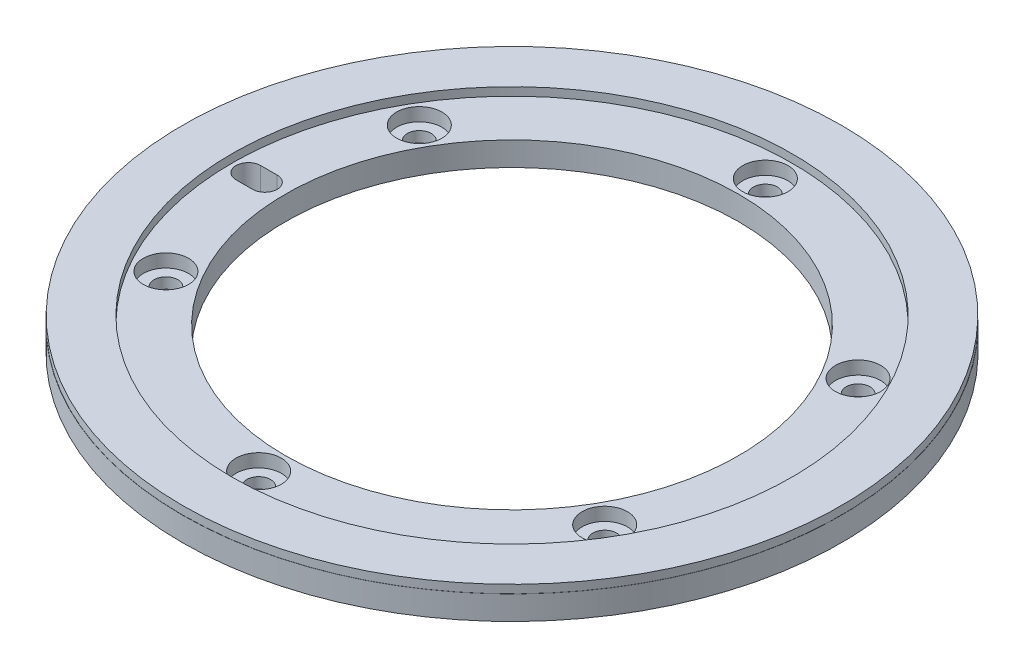
SolidWorks part; units mm, degrees
material "Chrome Stainless Steel"
ref_plane "Front Plane" through (0, 0, 0) normal (0, 0, 1) x (1, 0, 0)
ref_plane "Top Plane" through (0, 0, 0) normal (0, 1, 0) x (1, 0, 0)
ref_plane "Right Plane" through (0, 0, 0) normal (1, 0, 0) x (0, 0, -1)
sketch "Sketch1" plane through (0, 0, 0) normal (0, 0, 1) x (1, 0, 0)
  line L0 (0, -3.2439) -> (0, 13.5479) construction
  line L1 (-27.5, 0) -> (-40, 0)
  line L2 (-27.5, 0) -> (-27.5, 2.9)
  line L3 (-27.5, 2.9) -> (-40, 2.9)
  line L4 (-40, 0) -> (-40, 2.9)
  line L5 (-27.5, 0) -> (0, 0) construction
  dimension "D1" = 55
  dimension "D2" = 80
  dimension "D3" = 2.9
revolve "Revolve1" add sketch "Sketch1" angle 360 about L0
ref_plane "Plane1" through (0, 3.4, 0) normal (0, 1, 0) x (-1, 0, 0)
sketch "Sketch5" plane through (0, 2.9, 0) normal (0, 1, 0) x (1, 0, 0)
  circle A0 centre (0, 0) radius 34
  circle A1 centre (0, 0) radius 39.98
  dimension "D1" = 68
  dimension "D2" = 79.96
hole_wizard "CBORE for M2.5 Hex Socket Head Cap Screw2" positions "Sketch9" profile "Sketch8" counterbore size "M2.5" standard "DIN" end condition through all
sketch "Sketch9" plane through (0, 3.4, 0) normal (0, 1, 0) x (-1, 0, 0)
  line L0 (-46.9378, 0) -> (52.7339, 0) construction
  point P2 (0, -30.75)
  dimension "D1" = 61.5
sketch "Sketch8" plane through (0, 3.4, -30.75) normal (1, 0, 0) x (0, 0, 1)
  line L0 (0, 0) -> (0, 3.4)
  line L1 (0, 3.4) -> (1.45, 3.4)
  line L3 (1.45, 3.4) -> (1.45, 2.1)
  line L4 (1.45, 2.1) -> (2.75, 2.1)
  line L5 (2.75, 2.1) -> (2.75, 0)
  line L7 (2.75, 0) -> (0, 0)
  line L11 (0, -6.35) -> (0, 107.95) construction
  dimension "Thru Hole Dia." = 2.9
  dimension "Thru Hole Depth" = 3.4
  dimension "C'Bore Dia." = 5.5
  dimension "C'Bore Depth" = 2.1
pattern_circular "CirPattern1" count 6 over 360 about axis through (0, 0, 0) along (0, 1, 0) of "CBORE for M2.5 Hex Socket Head Cap Screw2"
sketch "Sketch10" plane through (0, 2.9, 0) normal (0, 1, 0) x (1, 0, 0)
  line L0 (-32, 0) -> (-30, 0) construction
  line L1 (-32, 1.5) -> (-30, 1.5)
  line L2 (-32, -1.5) -> (-30, -1.5)
  line L3 (0, 0) -> (-30, 0) construction
  arc A0 (-32, 1.5) -> (-32, -1.5) centre (-32, 0) ccw
  arc A1 (-30, -1.5) -> (-30, 1.5) centre (-30, 0) ccw
  point P3 (-31, 0)
  dimension "D1" = 32
  dimension "D2" = 3
  dimension "D3" = 2
extrude "Cut-Extrude4" cut sketch "Sketch10" against normal blind 10
extrude "Boss-Extrude1" add sketch "Sketch5" along normal blind 1
